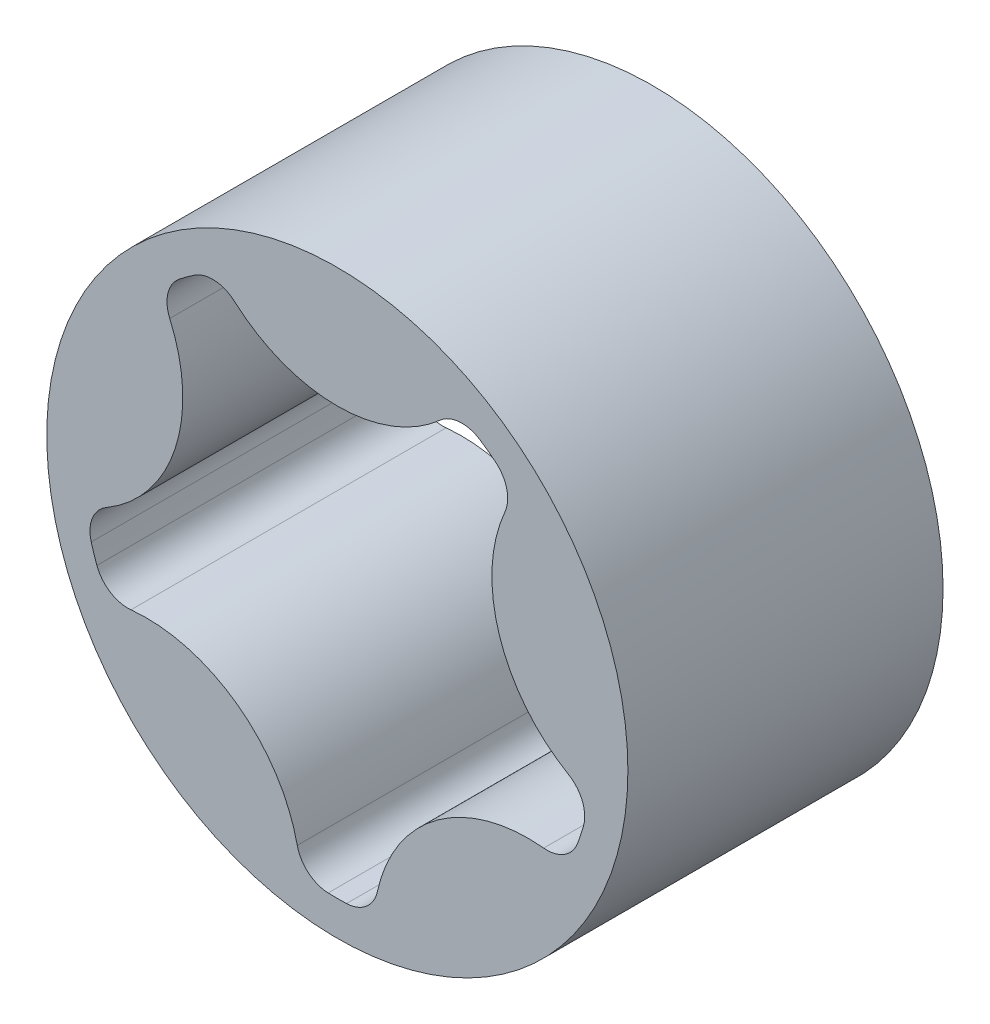
SolidWorks part; units mm, degrees
material "6061-T6 (SS)"
ref_plane "Plane1" through (0, 0, 0) normal (0, 0, 1) x (1, 0, 0)
ref_plane "Plane2" through (0, 0, 0) normal (0, 1, 0) x (-1, 0, 0)
ref_plane "Plane3" through (0, 0, 0) normal (1, 0, 0) x (0, 0, -1)
sketch "Sketch1" plane through (0, 0, 0) normal (0, 0, 1) x (1, 0, 0)
  line L0 (0, 0) -> (21.5444, 7.0002) construction
  line L1 (0, 0) -> (13.3151, -18.3267) construction
  line L2 (0, 0) -> (-13.3151, -18.3267) construction
  line L3 (0, 0) -> (-21.5444, 7.0002) construction
  line L4 (0, 0) -> (0, 22.6531) construction
  arc A0 (-9.9629, 14.8031) -> (-10.9999, 14.0497) centre (0, 0) ccw
  arc A1 (11.6837, 11.3305) -> (16.1122, -2.2991) centre (21.5444, 7.0002) ccw
  arc A2 (14.3864, -7.6105) -> (2.7924, -16.0341) centre (13.3151, -18.3267) ccw
  arc A3 (-2.7924, -16.0341) -> (-14.3864, -7.6105) centre (-13.3151, -18.3267) ccw
  arc A4 (-16.1122, -2.2991) -> (-11.6837, 11.3305) centre (-21.5444, 7.0002) ccw
  arc A5 (-7.1655, 14.6132) -> (7.1655, 14.6132) centre (0, 22.6531) ccw
  arc A6 (-17.1573, -4.9008) -> (-16.7612, -6.1199) centre (0, 0) ccw
  arc A7 (-0.6409, -17.832) -> (0.6409, -17.832) centre (0, 0) ccw
  arc A8 (16.7612, -6.1199) -> (17.1573, -4.9008) centre (0, 0) ccw
  arc A9 (10.9999, 14.0497) -> (9.9629, 14.8031) centre (0, 0) ccw
  circle A10 centre (0, 0) radius 20.2565
  arc A11 (-10.9999, 14.0497) -> (-11.6837, 11.3305) centre (-9.5906, 12.2497) ccw
  arc A12 (-7.1655, 14.6132) -> (-9.9629, 14.8031) centre (-8.6865, 12.9066) ccw
  arc A13 (9.9629, 14.8031) -> (7.1655, 14.6132) centre (8.6865, 12.9066) ccw
  arc A14 (11.6837, 11.3305) -> (10.9999, 14.0497) centre (9.5906, 12.2497) ccw
  arc A15 (17.1573, -4.9008) -> (16.1122, -2.2991) centre (14.9592, -4.273) ccw
  arc A16 (16.7612, -6.1199) -> (14.3864, -7.6105) centre (14.6138, -5.3359) cw
  arc A17 (2.7924, -16.0341) -> (0.6409, -17.832) centre (0.5588, -15.5475) cw
  arc A18 (-2.7924, -16.0341) -> (-0.6409, -17.832) centre (-0.5588, -15.5475) ccw
  arc A19 (-16.7612, -6.1199) -> (-14.3864, -7.6105) centre (-14.6138, -5.3359) ccw
  arc A20 (-16.1122, -2.2991) -> (-17.1573, -4.9008) centre (-14.9592, -4.273) ccw
  dimension "D1" = 72
  dimension "D6" = 35.687
  dimension "D7" = 10.7696
  dimension "D8" = 40.513
  dimension "D5" = 1.1176
  dimension "D9" = 2.286
  dimension "D2" = 72
  dimension "D3" = 72
  dimension "D4" = 72
extrude "Base-Extrude" add sketch "Sketch1" along normal blind 21.971
